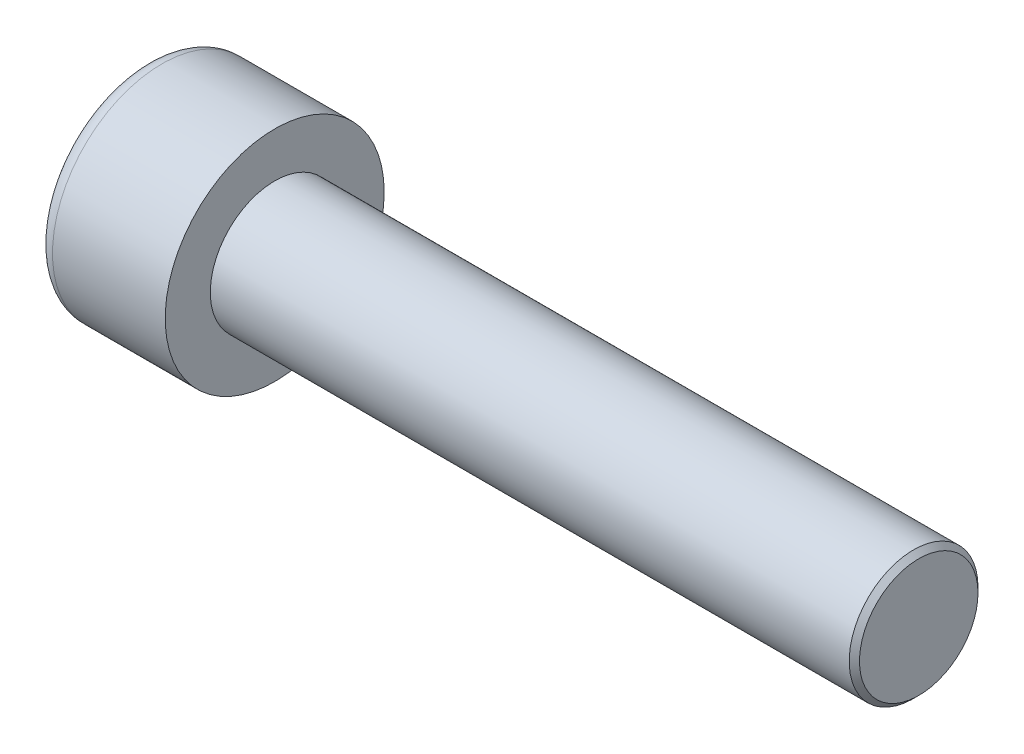
SolidWorks part; units mm, degrees
ref_plane "Front" through (0, 0, 0) normal (0, 0, 1) x (1, 0, 0)
ref_plane "Top" through (0, 0, 0) normal (0, 1, 0) x (1, 0, 0)
ref_plane "Right" through (0, 0, 0) normal (1, 0, 0) x (0, 0, -1)
sketch "Sketch1" plane through (0, 0, 0) normal (1, 0, 0) x (0, 0, -1)
  circle A0 centre (0, 0) radius 4.25
  dimension "dk" = 8.5
extrude "BaseHead" add sketch "Sketch1" along normal blind 5
sketch "Sketch2" plane through (5, 0, 0) normal (1, 0, 0) x (0, 0, -1)
  circle A0 centre (0, 0) radius 2.5
  dimension "d" = 5
extrude "BaseBody" add sketch "Sketch2" along normal blind 25
cosmetic thread "ThreadCosmetic1" [suppressed] parameters "b"=22, "D2"=4.134
sketch "Sketch3" plane through (0, 0, 0) normal (1, 0, 0) x (0, 0, -1)
  line L1 (2.3094, 0) -> (1.1547, 2)
  line L2 (1.1547, 2) -> (-1.1547, 2)
  line L3 (-1.1547, 2) -> (-2.3094, 0)
  line L4 (-2.3094, 0) -> (-1.1547, -2)
  line L5 (-1.1547, -2) -> (1.1547, -2)
  line L6 (1.1547, -2) -> (2.3094, 0)
  circle A0 centre (0, 0) radius 2 construction
  dimension "s" = 4
  dimension "e" = 4.6188
extrude "HexagonSocket" cut sketch "Sketch3" along normal blind 2.5
sketch "Sketch4" plane through (-4.1961, 0.75, 0) normal (0, 0, 1) x (-1, 0, 0)
  line L0 (-6.6961, 2.75) -> (-7.8508, 0.75)
  line L2 (-7.8508, 0.75) -> (-6.6961, 0.75)
  line L3 (-6.6961, 0.75) -> (-6.6961, 2.75)
  line L4 (-5.0351, 0.75) -> (0.839, 0.75) construction
  line L5 (-34.1961, 0.75) -> (-9.1961, 0.75) construction
  line L6 (-9.1961, 0.75) -> (-4.1961, 0.75) construction
  dimension "m" = 60
revolve "Cut-Revolve1" cut sketch "Sketch4" angle 360 about L4
fillet "HeadFillet" [suppressed] radius 0.2
fillet "TopFillet" radius 0.625 1 edges at (0, 0, -4.25)
chamfer "Chamfer1" distance 0.2 angle 45 1 edges at (30, 0, -2.5)
sketch "Sketch5" plane through (0, 0, 0) normal (0, 0, 1) x (1, 0, 0)
  line L0 (29.8, 2.125) -> (30.0165, 2.5)
  line L1 (30.0165, 2.5) -> (30.0165, 2.933)
  line L2 (30.0165, 2.933) -> (29.5835, 2.933)
  line L3 (29.5835, 2.933) -> (29.5835, 2.5)
  line L4 (29.5835, 2.5) -> (29.8, 2.125)
  line L5 (0, 0) -> (7.8886, 0) construction
  line L6 (29.8, -2.5) -> (29.8, 2.5) construction
  dimension "D1" = 5
  dimension "D2" = 0.433
revolve "Cut-Revolve10" [suppressed] cut sketch "Sketch5" angle 360 about L5
pattern_linear "LPattern10" [suppressed] count 42 spacing 0.5196 along (1, 0, 0)
equation "\"r1@TopFillet\" = \"d@Sketch2\" / 8"
equation "\"D1@Chamfer1\" = \"r@HeadFillet\""
equation "\"D1@Sketch5\" = \"d@Sketch2\""
equation "\"D2@Sketch5\" =  ( \"d@Sketch2\" - \"D2@ThreadCosmetic1\" )  / 2"
equation "\"D3@LPattern10\" = \"D2@Sketch5\" * 1.2"
equation "\"D1@LPattern10\" = \"b@ThreadCosmetic1\" / \"D3@LPattern10\""
